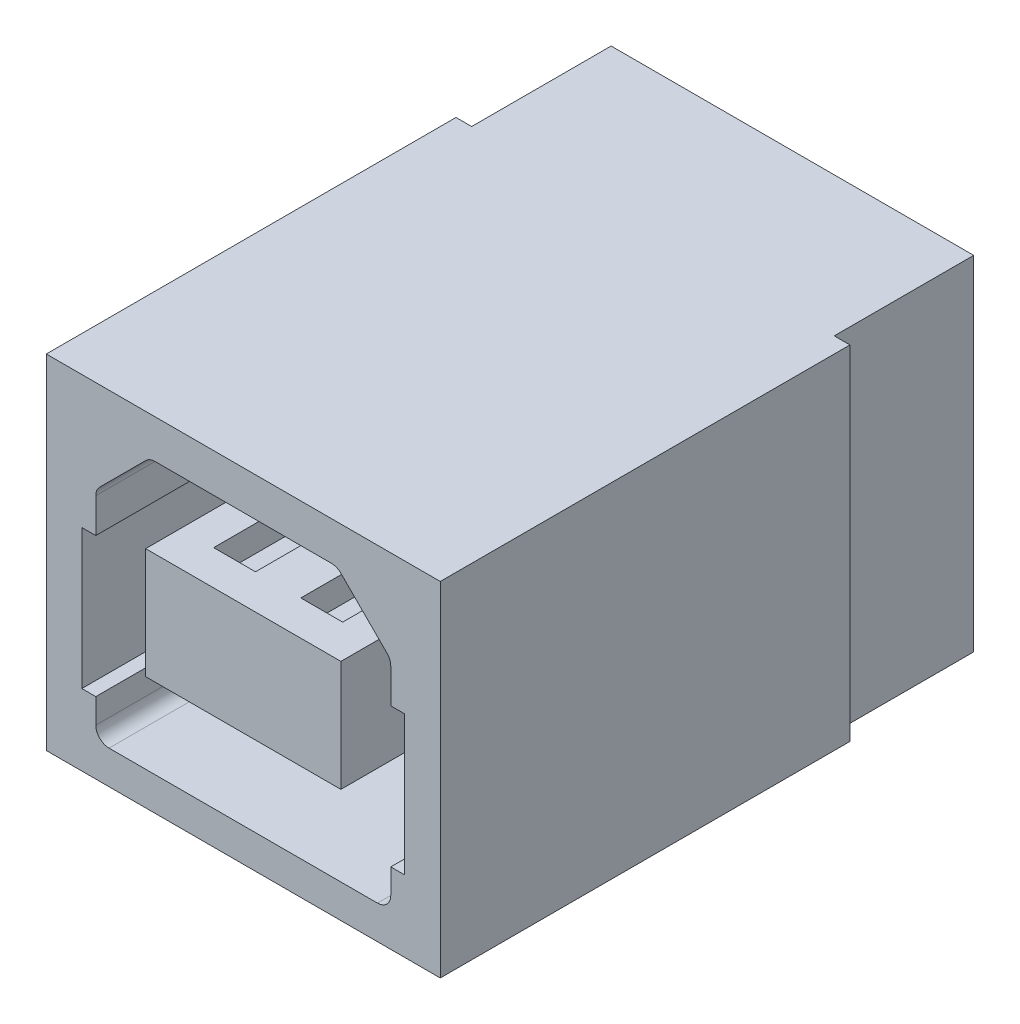
SolidWorks part; units mm, degrees
ref_plane "Plan de face" through (0, 0, 0) normal (0, 0, 1) x (1, 0, 0)
ref_plane "Plan de dessus" through (0, 0, 0) normal (0, 1, 0) x (1, 0, 0)
ref_plane "Plan de droite" through (0, 0, 0) normal (1, 0, 0) x (0, 0, -1)
sketch "Esquisse1" plane through (0, 0, 0) normal (0, 1, 0) x (1, 0, 0)
  line L0 (-5.65, 11.75) -> (-5.65, 0)
  line L1 (-5.65, 0) -> (5.65, 0)
  line L2 (5.65, 0) -> (5.65, 11.75)
  line L3 (5.65, 11.75) -> (5.2, 11.75)
  line L4 (5.2, 11.75) -> (5.2, 15.75)
  line L5 (5.2, 15.75) -> (-5.2, 15.75)
  line L6 (-5.2, 15.75) -> (-5.2, 11.75)
  line L7 (-5.2, 11.75) -> (-5.65, 11.75)
  dimension "D1" = 11.3
  dimension "D2" = 10.4
  dimension "D3" = 4
  dimension "D4" = 15.75
extrude "Boss.-Extru.1" add sketch "Esquisse1" along normal blind 9.85
sketch "Esquisse3" plane through (0, 0, 0) normal (0, 0, 1) x (1, 0, 0)
  line L0 (-4.63, 2.05) -> (-4.23, 2.05)
  line L1 (-4.23, 2.05) -> (-4.23, 1.34)
  line L2 (-3.85, 0.96) -> (3.85, 0.96)
  line L3 (-4.63, 2.05) -> (-4.63, 6.05)
  line L4 (-4.63, 6.05) -> (-4.23, 6.05)
  line L5 (-4.23, 6.05) -> (-4.23, 7.04)
  line L6 (-4.1187, 7.3087) -> (-2.7987, 8.6287)
  line L7 (-2.53, 8.74) -> (2.53, 8.74)
  line L8 (0, 8.74) -> (0, 0.96) construction
  line L9 (-5.65, 0) -> (5.65, 0) construction
  line L10 (4.1187, 7.3087) -> (2.7987, 8.6287)
  line L11 (4.23, 6.05) -> (4.23, 7.04)
  line L12 (4.63, 6.05) -> (4.23, 6.05)
  line L13 (4.63, 2.05) -> (4.63, 6.05)
  line L14 (4.23, 2.05) -> (4.23, 1.34)
  line L15 (4.63, 2.05) -> (4.23, 2.05)
  line L17 (-2.8, 6.44) -> (2.8, 6.44)
  line L18 (-2.8, 6.44) -> (-2.8, 3.26)
  line L19 (-2.8, 3.26) -> (2.8, 3.26)
  line L20 (2.8, 6.44) -> (2.8, 3.26)
  arc A0 (-4.23, 1.34) -> (-3.85, 0.96) centre (-3.85, 1.34) ccw
  arc A1 (-4.23, 7.04) -> (-4.1187, 7.3087) centre (-3.85, 7.04) cw
  arc A2 (-2.7987, 8.6287) -> (-2.53, 8.74) centre (-2.53, 8.36) cw
  arc A3 (2.7987, 8.6287) -> (2.53, 8.74) centre (2.53, 8.36) ccw
  arc A4 (4.23, 7.04) -> (4.1187, 7.3087) centre (3.85, 7.04) ccw
  arc A5 (4.23, 1.34) -> (3.85, 0.96) centre (3.85, 1.34) cw
  dimension "D2" = 0.38
  dimension "D1" = 0.96
  dimension "D3" = 135
  dimension "D4" = 7.78
  dimension "D5" = 4
  dimension "D6" = 2.05
  dimension "D7" = 8.46
  dimension "D8" = 0.4
  dimension "D9" = 1.7
  dimension "D10" = 5.6
  dimension "D11" = 3.18
  dimension "D12" = 2.3
extrude "Enlèv. mat.-Extru.1" cut sketch "Esquisse3" against normal blind 8.38
sketch "Esquisse4" plane through (0, 0, 0) normal (0, -1, 0) x (1, 0, 0)
  line L1 (-0.5, -7.5) -> (0.5, -7.5)
  line L2 (-0.5, -7.5) -> (-0.5, -15.75)
  line L3 (-0.5, -15.75) -> (0.5, -15.75)
  line L4 (0.5, -7.5) -> (0.5, -15.75)
  line L6 (-4.25, -6) -> (-3.25, -6)
  line L7 (-4.25, -6) -> (-4.25, -15.75)
  line L8 (-4.25, -15.75) -> (-3.25, -15.75)
  line L9 (-3.25, -6) -> (-3.25, -15.75)
  line L10 (3.25, -6) -> (4.25, -6)
  line L11 (3.25, -6) -> (3.25, -15.75)
  line L12 (3.25, -15.75) -> (4.25, -15.75)
  line L13 (4.25, -6) -> (4.25, -15.75)
  line L15 (5.2, -15.75) -> (-5.2, -15.75) construction
  line L16 (-5.65, 0) -> (5.65, 0) construction
  dimension "D1" = 6
  dimension "D2" = 1.5
  dimension "D3" = 1
  dimension "D4" = 8.5
  dimension "D5" = 4.25
  dimension "D6" = 0.5
extrude "Boss.-Extru.2" add sketch "Esquisse4" along normal blind 0.83
sketch "Esquisse5" plane through (0, 0, 0) normal (0, 0, -1) x (-1, 0, 0)
  line L0 (-2.8, 6.44) -> (2.8, 6.44) construction
  line L1 (1.85, 6.44) -> (0.65, 6.44)
  line L2 (1.85, 6.44) -> (1.85, 5.69)
  line L3 (1.85, 5.69) -> (0.65, 5.69)
  line L4 (0.65, 6.44) -> (0.65, 5.69)
  line L5 (2.8, 3.26) -> (-2.8, 3.26) construction
  line L6 (1.85, 3.26) -> (0.65, 3.26)
  line L7 (1.85, 3.26) -> (1.85, 4.01)
  line L8 (1.85, 4.01) -> (0.65, 4.01)
  line L9 (0.65, 3.26) -> (0.65, 4.01)
  line L10 (0, 6.44) -> (0, 3.26) construction
  line L11 (-2.8, 6.44) -> (2.8, 6.44) construction
  line L12 (2.8, 3.26) -> (-2.8, 3.26) construction
  line L13 (-0.65, 3.26) -> (-0.65, 4.01)
  line L14 (-1.85, 4.01) -> (-0.65, 4.01)
  line L15 (-1.85, 3.26) -> (-1.85, 4.01)
  line L16 (-1.85, 3.26) -> (-0.65, 3.26)
  line L17 (-0.65, 6.44) -> (-0.65, 5.69)
  line L18 (-1.85, 5.69) -> (-0.65, 5.69)
  line L19 (-1.85, 6.44) -> (-1.85, 5.69)
  line L20 (-1.85, 6.44) -> (-0.65, 6.44)
  dimension "D1" = 1.2
  dimension "D2" = 0.75
  dimension "D3" = 0.65
extrude "Enlèv. mat.-Extru.2" cut sketch "Esquisse5" along direction (0, 0, 1) on the side of the normal up to surface (14.75 mm away) from offset 1
sketch "Esquisse6" plane through (0, 0, -15.75) normal (0, 0, -1) x (-1, 0, 0)
  line L0 (-3.25, 0) -> (-0.5, 0) construction
  line L1 (-0.65, 6.44) -> (-1.85, 6.44)
  line L2 (-0.65, 6.44) -> (-0.65, 0)
  line L3 (-0.65, 0) -> (-1.85, 0)
  line L4 (-1.85, 6.44) -> (-1.85, 0)
  line L6 (0.65, 6.44) -> (1.85, 6.44)
  line L7 (0.65, 6.44) -> (0.65, 0)
  line L8 (0.65, 0) -> (1.85, 0)
  line L9 (1.85, 6.44) -> (1.85, 0)
  line L10 (1.85, 5.69) -> (1.85, 6.44) construction
extrude "Enlèv. mat.-Extru.3" cut sketch "Esquisse6" against normal blind 1.3
sketch "Esquisse7" plane through (0, 0, -14.45) normal (0, 0, -1) x (-1, 0, 0)
  line L0 (-1.85, 4.01) -> (-0.65, 4.01)
  line L1 (-0.65, 4.01) -> (-0.65, 2.26)
  line L2 (-0.65, 0) -> (-0.65, 3.26) construction
  line L3 (-0.65, 2.26) -> (-0.95, 2.26)
  line L4 (-0.95, 2.26) -> (-0.95, 0)
  line L5 (-1.85, 0) -> (-0.65, 0) construction
  line L6 (-0.95, 0) -> (-1.55, 0)
  line L7 (-1.55, 0) -> (-1.55, 2.26)
  line L8 (-1.55, 2.26) -> (-1.85, 2.26)
  line L9 (-1.85, 0) -> (-1.85, 6.44) construction
  line L10 (-1.85, 2.26) -> (-1.85, 4.01)
  line L11 (0.65, 2.26) -> (0.65, 4.01)
  line L12 (0.65, 0) -> (0.65, 6.44) construction
  line L13 (0.65, 4.01) -> (1.85, 4.01)
  line L14 (1.85, 4.01) -> (1.85, 2.26)
  line L15 (1.85, 2.26) -> (1.55, 2.26)
  line L16 (1.55, 2.26) -> (1.55, 0)
  line L17 (0.65, 0) -> (1.85, 0) construction
  line L18 (1.55, 0) -> (0.95, 0)
  line L19 (0.95, 0) -> (0.95, 2.26)
  line L20 (0.95, 2.26) -> (0.65, 2.26)
  dimension "D1" = 2.26
  dimension "D2" = 0.6
extrude "Enlèv. mat.-Extru.7" cut sketch "Esquisse7" against normal blind 1.3
